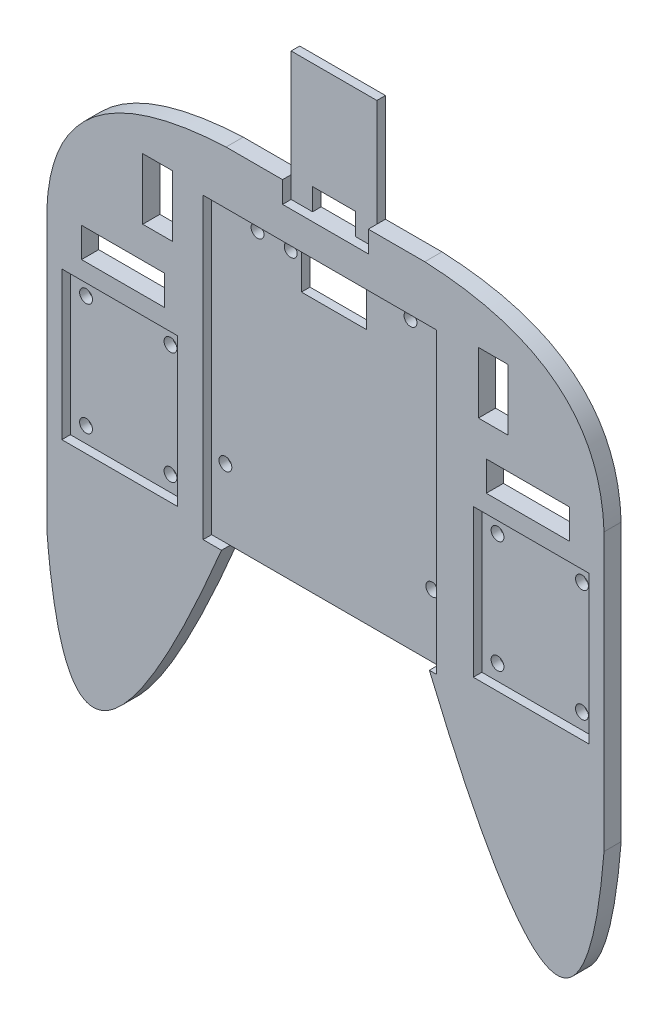
SolidWorks part; units mm, degrees
ref_plane "Ön Düzlem" through (0, 0, 0) normal (0, 0, 1) x (1, 0, 0)
ref_plane "Üst Düzlem" through (0, 0, 0) normal (0, 1, 0) x (1, 0, 0)
ref_plane "Sağ Düzlem" through (0, 0, 0) normal (1, 0, 0) x (0, 0, -1)
sketch "Çizim1" plane through (0, 0, 0) normal (0, 0, 1) x (1, 0, 0)
  line L1 (-65, -80) -> (65, -80)
  line L2 (-65, -80) -> (-65, 80)
  line L3 (-65, 80) -> (65, 80)
  line L4 (65, -80) -> (65, 80)
  line L5 (-65, -80) -> (65, 80) construction
  line L6 (-65, 80) -> (65, -80) construction
  point P0 (0, 0)
extrude "Yükseklik-Ekstrüzyon1" add sketch "Çizim1" along normal blind 4
sketch "Çizim3" plane through (0, 0, 0) normal (0, 0, -1) x (-1, 0, 0)
  line L0 (0, 80) -> (0, -80) construction
  line L1 (-65, 80) -> (65, 80) construction
  line L2 (65, -80) -> (-65, -80) construction
  line L3 (65, 80) -> (65, 55)
  line L4 (-65, 80) -> (-10, 80)
  line L5 (-65, 80) -> (-65, 55)
  line L6 (-65, 55) -> (-10, 55)
  line L7 (-10, 80) -> (-10, 55)
  line L8 (65, 80) -> (10, 80)
  line L9 (10, 80) -> (10, 55)
  line L10 (65, 55) -> (10, 55)
extrude "Kes-Ekstrüzyon1" cut sketch "Çizim3" against normal blind 4
sketch "Çizim4" plane through (0, 0, 4) normal (0, 0, 1) x (1, 0, 0)
  line L0 (0, 80) -> (0, -80) construction
  line L1 (10, 80) -> (-10, 80) construction
  line L2 (-65, -80) -> (65, -80) construction
  line L4 (-65, 55) -> (-65, -80) construction
  line L6 (-24.2494, -27.0064) -> (24.2494, -27.0064)
  line L7 (-65, -43.2449) -> (-65, -80)
  line L8 (-65, -80) -> (65, -80)
  line L9 (65, -80) -> (65, -43.2449)
  spline S0 degree 2 poles (-65, -43.2449) (-59.4852, -111.4317) (-24.2494, -27.0064) knots 0 0 0 1 1 1
  spline S1 degree 2 poles (65, -43.2449) (59.4852, -111.4317) (24.2494, -27.0064) knots 0 0 0 1 1 1
  point P8 (0, -27.0064)
extrude "Kes-Ekstrüzyon2" cut sketch "Çizim4" against normal blind 10
sketch "Çizim5" plane through (0, 0, 4) normal (0, 0, 1) x (1, 0, 0)
  line L1 (-28.548, 42.588) -> (25.4643, 42.588)
  line L2 (-28.548, 42.588) -> (-28.548, -26.3116)
  line L3 (-28.548, -26.3116) -> (25.4643, -26.3116)
  line L4 (25.4643, 42.588) -> (25.4643, -26.3116)
extrude "Kes-Ekstrüzyon3" cut sketch "Çizim5" against normal blind 2
sketch "Çizim8" plane through (0, 0, 4) normal (0, 0, 1) x (1, 0, 0)
  line L1 (-28.548, 42.588) -> (25.9217, 42.588)
  line L2 (-28.548, 42.588) -> (-28.548, -27.0064)
  line L3 (-28.548, -27.0064) -> (25.9217, -27.0064)
  line L4 (25.9217, 42.588) -> (25.9217, -27.0064)
extrude "Kes-Ekstrüzyon5" cut sketch "Çizim8" against normal blind 2
sketch "Çizim9" plane through (0, 0, 4) normal (0, 0, 1) x (1, 0, 0)
  circle A0 centre (-10.0957, 39.7284) radius 1.5
  circle A1 centre (17.8443, 39.7284) radius 1.5
  circle A2 centre (-25.3357, -11.0716) radius 1.5
  circle A3 centre (22.9243, -12.3416) radius 1.5
extrude "Kes-Ekstrüzyon6" cut sketch "Çizim9" against normal blind 5
sketch "Çizim10" plane through (0, 0, 4) normal (0, 0, 1) x (1, 0, 0)
  line L0 (-61.5, -7) -> (-61.5, -46.5) construction
  line L1 (-61.5, 11.2129) -> (-34.5, 11.2129)
  line L2 (-61.5, 11.2129) -> (-61.5, -23.2871)
  line L3 (-61.5, -23.2871) -> (-34.5, -23.2871)
  line L4 (-34.5, 11.2129) -> (-34.5, -23.2871)
  line L5 (0, 80) -> (0, -27.0064) construction
  line L6 (10, 80) -> (-10, 80) construction
  line L7 (-24.2494, -27.0064) -> (24.2494, -27.0064) construction
  line L8 (61.5, -23.2871) -> (34.5, -23.2871)
  line L9 (61.5, 11.2129) -> (61.5, -23.2871)
  line L10 (34.5, 11.2129) -> (34.5, -23.2871)
  line L11 (61.5, 11.2129) -> (34.5, 11.2129)
extrude "Kes-Ekstrüzyon7" cut sketch "Çizim10" against normal blind 2
sketch "Çizim11" plane through (0, 0, 4) normal (0, 0, 1) x (1, 0, 0)
  line L0 (-57.85, 6.5629) -> (-38.15, 6.5629)
  line L2 (-48, 11.2129) -> (-48, 6.5629)
  line L3 (-34.5, 11.2129) -> (-61.5, 11.2129) construction
  line L4 (-38.15, 6.5629) -> (-38.15, -19.6371)
  line L5 (-38.15, -19.6371) -> (-57.85, -19.6371)
  line L6 (0, 80) -> (0, -27.3883) construction
  line L7 (10, 80) -> (-10, 80) construction
  circle A0 centre (-57.85, 6.5629) radius 1.5
  circle A1 centre (-38.15, 6.5629) radius 1.5
  circle A2 centre (-38.15, -19.6371) radius 1.5
  circle A3 centre (-57.85, -19.6371) radius 1.5
  circle A4 centre (57.85, -19.6371) radius 1.5
  circle A5 centre (38.15, -19.6371) radius 1.5
  circle A6 centre (38.15, 6.5629) radius 1.5
  circle A7 centre (57.85, 6.5629) radius 1.5
  point P3 (-48, 6.5629)
extrude "Kes-Ekstrüzyon8" cut sketch "Çizim11" against normal blind 5
sketch "Çizim12" plane through (0, 0, 4) normal (0, 0, 1) x (1, 0, 0)
  line L0 (0, 80) -> (0, -27.0064)
  line L1 (10, 80) -> (-10, 80) construction
  line L2 (-24.2494, -27.0064) -> (24.2494, -27.0064) construction
  line L5 (-65, 55) -> (-65, -43.2449) construction
  line L6 (-65, 21.3127) -> (-65, 55)
  line L7 (-10, 55) -> (-65, 55) construction
  line L8 (65, 21.3127) -> (65, 55)
  line L12 (-65, 55) -> (-12.4407, 55)
  line L13 (65, 55) -> (12.4407, 55)
  spline S0 degree 2 poles (-65, 21.3127) (-63.8334, 57.0918) (-12.4407, 55) knots 0 0 0 1 1 1
  spline S1 degree 2 poles (65, 21.3127) (63.8334, 57.0918) (12.4407, 55) knots 0 0 0 1 1 1
  line M20 (65, -43.2449) -> (65, 55)
  line M21 (65, 55) -> (10, 55)
  line M26 (-65, 55) -> (-65, -43.2449)
extrude "Kes-Ekstrüzyon9" cut sketch "Çizim12" against normal blind 5 and the other way through all contours S0 L12 M26 | S1 M20 M21
sketch "Çizim13" plane through (0, 0, 4) normal (0, 0, 1) x (1, 0, 0)
  line L0 (0, 80) -> (0, 50)
  line L1 (10, 80) -> (-10, 80) construction
  line L3 (-10, 80) -> (10, 80)
  line L4 (-10, 80) -> (-10, 50)
  line L5 (-10, 50) -> (10, 50)
  line L6 (10, 80) -> (10, 50)
  line M26 (10, 55) -> (10, 80)
  line M27 (10, 80) -> (-10, 80)
  line M28 (-10, 80) -> (-10, 55)
extrude "Kes-Ekstrüzyon10" cut sketch "Çizim13" against normal blind 2 contours L4 L5 L0 M27 M28 | L6 L0 L5 M26 M27
sketch "Çizim14" plane through (0, 0, 2) normal (0, 0, 1) x (1, 0, 0)
  line L0 (0, 50) -> (0, 55.1)
  line L1 (-10, 50) -> (10, 50) construction
  line L2 (0, 55.1) -> (5, 55.1)
  line L3 (0, 55.1) -> (-5, 55.1)
  line L4 (-5, 55.1) -> (-5, 50)
  line L5 (-5, 50) -> (0, 50)
  line L6 (0, 50) -> (5, 50)
  line L7 (5, 50) -> (5, 55.1)
  line M8 (-10, 50) -> (10, 50)
extrude "Kes-Ekstrüzyon11" cut sketch "Çizim14" against normal blind 9 contours L3 L4 L0 M8 | L7 L2 L0 M8
sketch "Çizim15" plane through (0, 0, 4) normal (0, 0, 1) x (1, 0, 0)
  line L0 (0, 80) -> (0, -27.0064)
  line L1 (10, 80) -> (-10, 80) construction
  line L2 (-24.2494, -27.0064) -> (24.2494, -27.0064) construction
  line L3 (56.9008, 22.3324) -> (56.9008, 15.3983)
  line L4 (-56.9008, 22.3324) -> (-37.5259, 22.3324)
  line L5 (-56.9008, 22.3324) -> (-56.9008, 15.3983)
  line L6 (-56.9008, 15.3983) -> (-37.5259, 15.3983)
  line L7 (-37.5259, 22.3324) -> (-37.5259, 15.3983)
  line L8 (56.9008, 22.3324) -> (37.5259, 22.3324)
  line L9 (37.5259, 22.3324) -> (37.5259, 15.3983)
  line L10 (56.9008, 15.3983) -> (37.5259, 15.3983)
  line L11 (42.6246, 43.9506) -> (42.6246, 29.6744)
  line L12 (-42.6246, 43.9506) -> (-35.6904, 43.9506)
  line L13 (-42.6246, 43.9506) -> (-42.6246, 29.6744)
  line L14 (-42.6246, 29.6744) -> (-35.6904, 29.6744)
  line L15 (-35.6904, 43.9506) -> (-35.6904, 29.6744)
  line L16 (42.6246, 43.9506) -> (35.6904, 43.9506)
  line L17 (35.6904, 43.9506) -> (35.6904, 29.6744)
  line L18 (42.6246, 29.6744) -> (35.6904, 29.6744)
extrude "Kes-Ekstrüzyon12" cut sketch "Çizim15" against normal blind 9 contours L15 L12 L13 L14 | L7 L4 L5 L6 | L18 L11 L16 L17 | L8 L9 L10 L3
sketch "Çizim16" plane through (0, 0, 2) normal (0, 0, 1) x (1, 0, 0)
  line L0 (0, -27.0064) -> (0, 80)
  circle A0 centre (17.8443, 39.7284) radius 1.5
  circle A1 centre (-17.8443, 39.7284) radius 1.5
extrude "Kes-Ekstrüzyon13" cut sketch "Çizim16" against normal blind 10 contours A1
sketch "Çizim17" plane through (0, 0, 2) normal (0, 0, 1) x (1, 0, 0)
  line L0 (0, -27.0064) -> (0, 42.588)
  line L1 (0, 40.7882) -> (7.6, 40.7882)
  line L2 (0, 40.7882) -> (-7.6, 40.7882)
  line L4 (-7.6, 40.7882) -> (7.6, 40.7882)
  line L5 (-7.6, 40.7882) -> (-7.6, 32.4882)
  line L6 (-7.6, 32.4882) -> (7.6, 32.4882)
  line L7 (7.6, 40.7882) -> (7.6, 32.4882)
extrude "Kes-Ekstrüzyon14" cut sketch "Çizim17" against normal blind 10 contours L5 L6 L0 L2 | L7 L1 L0 L6
